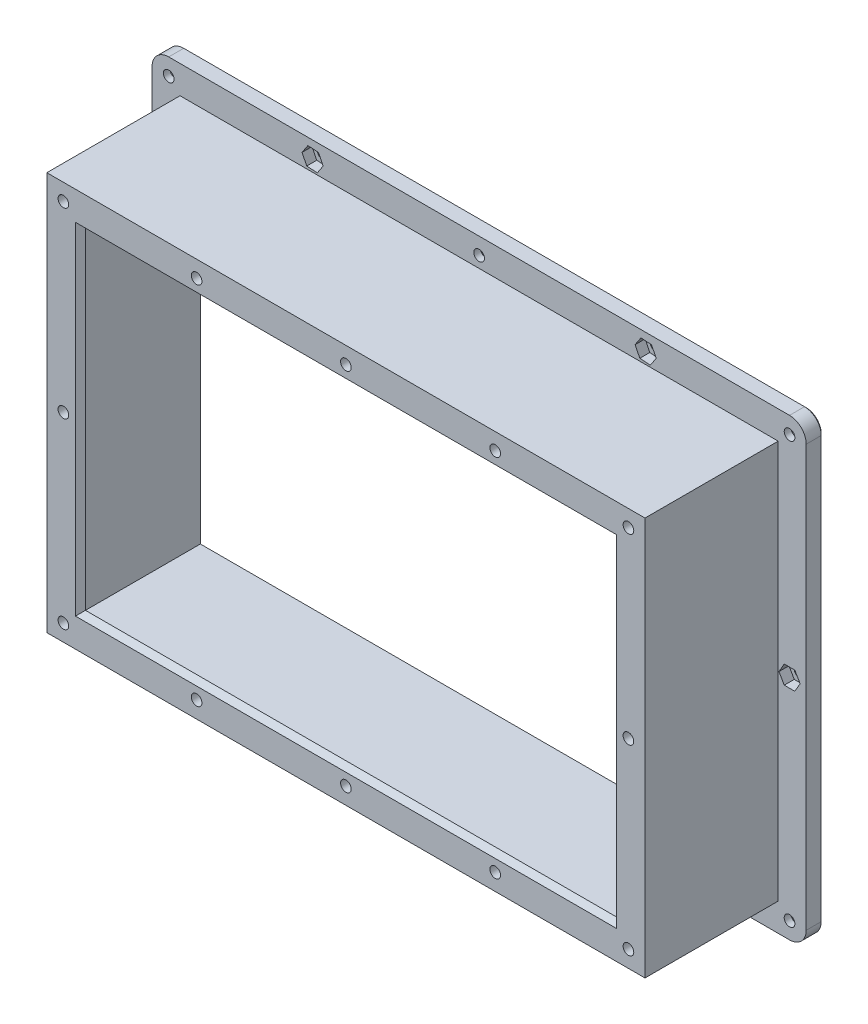
SolidWorks part; units mm, degrees
ref_plane "Alzado" through (0, 0, 0) normal (0, 0, 1) x (1, 0, 0)
ref_plane "Planta" through (0, 0, 0) normal (0, 1, 0) x (1, 0, 0)
ref_plane "Vista lateral" through (0, 0, 0) normal (1, 0, 0) x (0, 0, -1)
sketch "Croquis1" plane through (0, 0, 0) normal (0, 0, 1) x (1, 0, 0)
  line L1 (-89.8, 59.8) -> (89.8, 59.8)
  line L2 (-89.8, 59.8) -> (-89.8, -59.8)
  line L3 (-89.8, -59.8) -> (89.8, -59.8)
  line L4 (89.8, 59.8) -> (89.8, -59.8)
  line L5 (-89.8, 59.8) -> (89.8, -59.8) construction
  line L6 (-89.8, -59.8) -> (89.8, 59.8) construction
  line L7 (-88.2, 58.2) -> (88.2, 58.2)
  line L8 (-88.2, 58.2) -> (-88.2, -58.2)
  line L9 (-88.2, -58.2) -> (88.2, -58.2)
  line L10 (88.2, 58.2) -> (88.2, -58.2)
  line L11 (-88.2, 58.2) -> (88.2, -58.2) construction
  line L12 (-88.2, -58.2) -> (88.2, 58.2) construction
  point P0 (0, 0)
  point P6 (0, 0)
  dimension "D1" = 179.6
  dimension "D2" = 119.6
  dimension "D3" = 1.6
  dimension "D4" = 1.6
extrude "Saliente-Extruir1" add sketch "Croquis1" along normal blind 40
sketch "Croquis2" plane through (0, 0, 0) normal (0, 0, -1) x (-1, 0, 0)
  line L1 (-98.2, 68.2) -> (98.2, 68.2)
  line L2 (-98.2, 68.2) -> (-98.2, -68.2)
  line L3 (-98.2, -68.2) -> (98.2, -68.2)
  line L4 (98.2, 68.2) -> (98.2, -68.2)
  line L5 (-98.2, 68.2) -> (98.2, -68.2) construction
  line L6 (-98.2, -68.2) -> (98.2, 68.2) construction
  line L7 (-88.2, 58.2) -> (88.2, 58.2)
  line L8 (-88.2, 58.2) -> (-88.2, -58.2)
  line L9 (-88.2, -58.2) -> (88.2, -58.2)
  line L10 (88.2, 58.2) -> (88.2, -58.2)
  line L11 (-88.2, 58.2) -> (88.2, -58.2) construction
  line L12 (-88.2, -58.2) -> (88.2, 58.2) construction
  point P1 (0, 0)
  point P6 (0, 0)
  dimension "D1" = 10
  dimension "D2" = 10
extrude "Saliente-Extruir2" add sketch "Croquis2" along normal blind 5
sketch "Croquis3" plane through (0, 58.2, 0) normal (0, -1, 0) x (1, 0, 0)
  line L0 (0, 0) -> (0, 50000) construction
  line L1 (-88.2, 45) -> (-88.2, 50045) construction
  line L2 (-88.2, 30) -> (-78.2, 40)
  line L3 (-89.8, 40) -> (89.8, 40) construction
  line L4 (-78.2, 40) -> (-88.2, 40)
  line L5 (-88.2, 40) -> (-88.2, 30)
  line L6 (88.2, 40) -> (88.2, 30)
  line L7 (78.2, 40) -> (88.2, 40)
  line L8 (88.2, 30) -> (78.2, 40)
  dimension "D1" = 10
extrude "Saliente-Extruir3" add sketch "Croquis3" along normal up to surface (116.4 mm away) up to face at (0, -58.2, 17.5)
sketch "Croquis4" plane through (-88.2, 0, 0) normal (1, 0, 0) x (0, 0, -1)
  line L0 (-40, 58.2) -> (-30, 58.2)
  line L1 (-30, -58.2) -> (-30, 58.2) construction
  line L2 (-40, 58.2) -> (-30, 58.2) construction
  line L3 (-30, 58.2) -> (-40, 48.2)
  line L4 (-40, -59.8) -> (-40, 59.8) construction
  line L5 (-40, 48.2) -> (-40, 58.2)
  line L6 (0, 0) -> (-50000, 0) construction
  line L7 (-40, -48.2) -> (-40, -58.2)
  line L8 (-30, -58.2) -> (-40, -48.2)
  line L9 (-40, -58.2) -> (-30, -58.2)
extrude "Saliente-Extruir4" add sketch "Croquis4" along normal up to surface (176.4 mm away) up to face at (88.2, 0, 12.5)
sketch "Croquis5" plane through (0, 0, 40) normal (0, 0, 1) x (1, 0, 0)
  line L0 (-90, 54.8) -> (49910, 54.8) construction
  line L3 (89.8, 59.8) -> (-89.8, 59.8) construction
  line L4 (0, 0) -> (0, 50000) construction
  line L5 (0, 0) -> (50000, 0) construction
  circle A0 centre (-84.8273, 54.8) radius 1.6
  circle A1 centre (0, 54.8) radius 1.6
  circle A2 centre (-44.8273, 54.8) radius 1.6
  circle A3 centre (44.8273, 54.8) radius 1.6
  circle A4 centre (84.8273, 54.8) radius 1.6
  circle A5 centre (84.8273, -54.8) radius 1.6
  circle A6 centre (44.8273, -54.8) radius 1.6
  circle A7 centre (-44.8273, -54.8) radius 1.6
  circle A8 centre (0, -54.8) radius 1.6
  circle A9 centre (-84.8273, -54.8) radius 1.6
  circle A10 centre (-84.8273, 0) radius 1.6
  circle A11 centre (84.8273, 0) radius 1.6
  dimension "D2" = 3.2
  dimension "D1" = 5
  dimension "D3" = 40
extrude "Cortar-Extruir1" cut sketch "Croquis5" against normal through all
sketch "Croquis6" plane through (0, 0, 40) normal (0, 0, 1) x (1, 0, 0)
  line L0 (0, 0) -> (50000, 0) construction
  line L1 (3.1754, 54.8) -> (1.5877, 57.55)
  line L2 (1.5877, 57.55) -> (-1.5877, 57.55)
  line L3 (-1.5877, 57.55) -> (-3.1754, 54.8)
  line L4 (-3.1754, 54.8) -> (-1.5877, 52.05)
  line L5 (-1.5877, 52.05) -> (1.5877, 52.05)
  line L6 (1.5877, 52.05) -> (3.1754, 54.8)
  line L7 (-41.6519, 54.8) -> (-43.2396, 57.55)
  line L8 (-43.2396, 57.55) -> (-46.4151, 57.55)
  line L9 (-46.4151, 57.55) -> (-48.0028, 54.8)
  line L10 (-48.0028, 54.8) -> (-46.4151, 52.05)
  line L11 (-46.4151, 52.05) -> (-43.2396, 52.05)
  line L12 (-43.2396, 52.05) -> (-41.6519, 54.8)
  line L13 (-81.6519, 54.8) -> (-83.2396, 57.55)
  line L14 (-83.2396, 57.55) -> (-86.4151, 57.55)
  line L15 (-86.4151, 57.55) -> (-88.0028, 54.8)
  line L16 (-88.0028, 54.8) -> (-86.4151, 52.05)
  line L17 (-86.4151, 52.05) -> (-83.2396, 52.05)
  line L18 (-83.2396, 52.05) -> (-81.6519, 54.8)
  line L19 (48.0028, 54.8) -> (46.4151, 57.55)
  line L20 (46.4151, 57.55) -> (43.2396, 57.55)
  line L21 (43.2396, 57.55) -> (41.6519, 54.8)
  line L22 (41.6519, 54.8) -> (43.2396, 52.05)
  line L23 (43.2396, 52.05) -> (46.4151, 52.05)
  line L24 (46.4151, 52.05) -> (48.0028, 54.8)
  line L25 (88.0028, 54.8) -> (86.4151, 57.55)
  line L26 (86.4151, 57.55) -> (83.2396, 57.55)
  line L27 (83.2396, 57.55) -> (81.6519, 54.8)
  line L28 (81.6519, 54.8) -> (83.2396, 52.05)
  line L29 (83.2396, 52.05) -> (86.4151, 52.05)
  line L30 (86.4151, 52.05) -> (88.0028, 54.8)
  line L31 (86.4151, -52.05) -> (88.0028, -54.8)
  line L32 (83.2396, -52.05) -> (86.4151, -52.05)
  line L33 (81.6519, -54.8) -> (83.2396, -52.05)
  line L34 (83.2396, -57.55) -> (81.6519, -54.8)
  line L35 (86.4151, -57.55) -> (83.2396, -57.55)
  line L36 (88.0028, -54.8) -> (86.4151, -57.55)
  line L37 (46.4151, -52.05) -> (48.0028, -54.8)
  line L38 (43.2396, -52.05) -> (46.4151, -52.05)
  line L39 (41.6519, -54.8) -> (43.2396, -52.05)
  line L40 (43.2396, -57.55) -> (41.6519, -54.8)
  line L41 (46.4151, -57.55) -> (43.2396, -57.55)
  line L42 (48.0028, -54.8) -> (46.4151, -57.55)
  line L43 (-83.2396, -52.05) -> (-81.6519, -54.8)
  line L44 (-86.4151, -52.05) -> (-83.2396, -52.05)
  line L45 (-88.0028, -54.8) -> (-86.4151, -52.05)
  line L46 (-86.4151, -57.55) -> (-88.0028, -54.8)
  line L47 (-83.2396, -57.55) -> (-86.4151, -57.55)
  line L48 (-81.6519, -54.8) -> (-83.2396, -57.55)
  line L49 (-43.2396, -52.05) -> (-41.6519, -54.8)
  line L50 (-46.4151, -52.05) -> (-43.2396, -52.05)
  line L51 (-48.0028, -54.8) -> (-46.4151, -52.05)
  line L52 (-46.4151, -57.55) -> (-48.0028, -54.8)
  line L53 (-43.2396, -57.55) -> (-46.4151, -57.55)
  line L54 (-41.6519, -54.8) -> (-43.2396, -57.55)
  line L55 (1.5877, -52.05) -> (3.1754, -54.8)
  line L56 (-1.5877, -52.05) -> (1.5877, -52.05)
  line L57 (-3.1754, -54.8) -> (-1.5877, -52.05)
  line L58 (-1.5877, -57.55) -> (-3.1754, -54.8)
  line L59 (1.5877, -57.55) -> (-1.5877, -57.55)
  line L60 (3.1754, -54.8) -> (1.5877, -57.55)
  line L62 (-81.6519, 0) -> (-83.2396, 2.75)
  line L63 (-83.2396, 2.75) -> (-86.4151, 2.75)
  line L64 (-86.4151, 2.75) -> (-88.0028, 0)
  line L65 (-88.0028, 0) -> (-86.4151, -2.75)
  line L66 (-86.4151, -2.75) -> (-83.2396, -2.75)
  line L67 (-83.2396, -2.75) -> (-81.6519, 0)
  line L68 (88.0028, 0) -> (86.4151, 2.75)
  line L69 (86.4151, 2.75) -> (83.2396, 2.75)
  line L70 (83.2396, 2.75) -> (81.6519, 0)
  line L71 (81.6519, 0) -> (83.2396, -2.75)
  line L72 (83.2396, -2.75) -> (86.4151, -2.75)
  line L73 (86.4151, -2.75) -> (88.0028, 0)
  circle A0 centre (0, 54.8) radius 2.75 construction
  circle A1 centre (-44.8273, 54.8) radius 2.75 construction
  circle A2 centre (-84.8273, 54.8) radius 2.75 construction
  circle A3 centre (44.8273, 54.8) radius 2.75 construction
  circle A4 centre (84.8273, 54.8) radius 2.75 construction
  circle A5 centre (84.8273, -54.8) radius 2.75 construction
  circle A6 centre (44.8273, -54.8) radius 2.75 construction
  circle A7 centre (-84.8273, -54.8) radius 2.75 construction
  circle A8 centre (-44.8273, -54.8) radius 2.75 construction
  circle A9 centre (0, -54.8) radius 2.75 construction
  circle A10 centre (-84.8273, 0) radius 2.75 construction
  circle A11 centre (84.8273, 0) radius 2.75 construction
  dimension "D1" = 5.5
extrude "Cortar-Extruir2" cut sketch "Croquis6" against normal through all from offset 3 offset against normal yes
chamfer "Chaflán1" distance 3 angle 45 4 edges at (-78.2, 0, 40) (0, -48.2, 40) (0, 48.2, 40) (78.2, 0, 40)
sketch "Croquis7" plane through (0, 0, -5) normal (0, 0, -1) x (-1, 0, 0)
  line L0 (0, 0) -> (0, 50000) construction
  line L1 (0, 0) -> (50000, 0) construction
  line L2 (0, 63.2) -> (50000, 63.2) construction
  line L3 (93.2, 64.2122) -> (93.2, -49935.7878) construction
  line L4 (98.2, 68.2) -> (-98.2, 68.2) construction
  line L5 (98.2, -68.2) -> (98.2, 68.2) construction
  circle A0 centre (0, 63.2) radius 1.6
  circle A2 centre (93.2, 63.2) radius 1.6
  circle A3 centre (93.2, 0) radius 1.6
  circle A4 centre (50, 63.2) radius 1.6
  circle A5 centre (-50, 63.2) radius 1.6
  circle A6 centre (-93.2, 63.2) radius 1.6
  circle A7 centre (-93.2, 0) radius 1.6
  circle A8 centre (-93.2, -63.2) radius 1.6
  circle A9 centre (-50, -63.2) radius 1.6
  circle A10 centre (50, -63.2) radius 1.6
  circle A11 centre (93.2, -63.2) radius 1.6
  circle A12 centre (0, -63.2) radius 1.6
  dimension "D3" = 3.2
  dimension "D1" = 5
  dimension "D2" = 5
  dimension "D4" = 100
extrude "Cortar-Extruir3" cut sketch "Croquis7" against normal through all
sketch "Croquis8" plane through (0, 0, -5) normal (0, 0, -1) x (-1, 0, 0)
  circle A0 centre (-93.2, 63.2) radius 2.75
  circle A1 centre (0, 63.2) radius 2.75
  circle A2 centre (93.2, 63.2) radius 2.75
  circle A3 centre (93.2, -63.2) radius 2.75
  circle A4 centre (0, -63.2) radius 2.75
  circle A5 centre (-93.2, -63.2) radius 2.75
  dimension "D1" = 5.5
extrude "Cortar-Extruir4" cut sketch "Croquis8" against normal blind 3
sketch "Croquis9" plane through (0, 0, -5) normal (0, 0, -1) x (-1, 0, 0)
  line L1 (-46.8309, 63.3996) -> (-48.5883, 66.0444)
  line L2 (-48.5883, 66.0444) -> (-51.7574, 65.8448)
  line L3 (-51.7574, 65.8448) -> (-53.1691, 63.0004)
  line L4 (-53.1691, 63.0004) -> (-51.4117, 60.3556)
  line L5 (-51.4117, 60.3556) -> (-48.2426, 60.5552)
  line L6 (-48.2426, 60.5552) -> (-46.8309, 63.3996)
  line L7 (53.1691, 63.3996) -> (51.4117, 66.0444)
  line L8 (51.4117, 66.0444) -> (48.2426, 65.8448)
  line L9 (48.2426, 65.8448) -> (46.8309, 63.0004)
  line L10 (46.8309, 63.0004) -> (48.5883, 60.3556)
  line L11 (48.5883, 60.3556) -> (51.7574, 60.5552)
  line L12 (51.7574, 60.5552) -> (53.1691, 63.3996)
  line L13 (53.1691, -63.3996) -> (51.7574, -60.5552)
  line L14 (51.7574, -60.5552) -> (48.5883, -60.3556)
  line L15 (48.5883, -60.3556) -> (46.8309, -63.0004)
  line L16 (46.8309, -63.0004) -> (48.2426, -65.8448)
  line L17 (48.2426, -65.8448) -> (51.4117, -66.0444)
  line L18 (51.4117, -66.0444) -> (53.1691, -63.3996)
  line L19 (-46.9644, -62.2681) -> (-49.2893, -60.1051)
  line L20 (-49.2893, -60.1051) -> (-52.3249, -61.0371)
  line L21 (-52.3249, -61.0371) -> (-53.0356, -64.1319)
  line L22 (-53.0356, -64.1319) -> (-50.7107, -66.2949)
  line L23 (-50.7107, -66.2949) -> (-47.6751, -65.3629)
  line L24 (-47.6751, -65.3629) -> (-46.9644, -62.2681)
  line L25 (96.3754, 0) -> (94.7877, 2.75)
  line L26 (94.7877, 2.75) -> (91.6123, 2.75)
  line L27 (91.6123, 2.75) -> (90.0246, 0)
  line L28 (90.0246, 0) -> (91.6123, -2.75)
  line L29 (91.6123, -2.75) -> (94.7877, -2.75)
  line L30 (94.7877, -2.75) -> (96.3754, 0)
  line L31 (-90.0246, 0) -> (-91.6123, 2.75)
  line L32 (-91.6123, 2.75) -> (-94.7877, 2.75)
  line L33 (-94.7877, 2.75) -> (-96.3754, 0)
  line L34 (-96.3754, 0) -> (-94.7877, -2.75)
  line L35 (-94.7877, -2.75) -> (-91.6123, -2.75)
  line L36 (-91.6123, -2.75) -> (-90.0246, 0)
  circle A0 centre (-50, 63.2) radius 2.75 construction
  circle A1 centre (50, 63.2) radius 2.75 construction
  circle A2 centre (50, -63.2) radius 2.75 construction
  circle A3 centre (-50, -63.2) radius 2.75 construction
  circle A4 centre (93.2, 0) radius 2.75 construction
  circle A5 centre (-93.2, 0) radius 2.75 construction
  dimension "D1" = 5.5
extrude "Cortar-Extruir5" cut sketch "Croquis9" against normal through all from offset 2 offset against normal yes
fillet "Redondeo1" radius 5 4 edges at (98.2, 68.2, -2.5) (98.2, -68.2, -2.5) (-98.2, -68.2, -2.5) (-98.2, 68.2, -2.5)
chamfer "Chaflán2" distance 0.5 angle 45 24 edges at (88.2, 0, -5) (0, -58.2, -5) (-88.2, 0, -5) (0, 58.2, -5) (-96.7355, 66.7355, -5) (-98.2, 0, -5) (-96.7355, -66.7355, -5) (0, -68.2, -5) (96.7355, -66.7355, -5) (98.2, 0, -5) (96.7355, 66.7355, -5) (0, 68.2, -5) (-48.4, -63.2, -5) (-94.8, 0, -5) (-51.6, 63.2, -5) (51.6, 63.2, -5) (94.8, 0, -5) (48.4, -63.2, -5) (90.45, 63.2, -5) (-2.75, 63.2, -5) (-95.95, 63.2, -5) (-95.95, -63.2, -5) (-2.75, -63.2, -5) (90.45, -63.2, -5)
